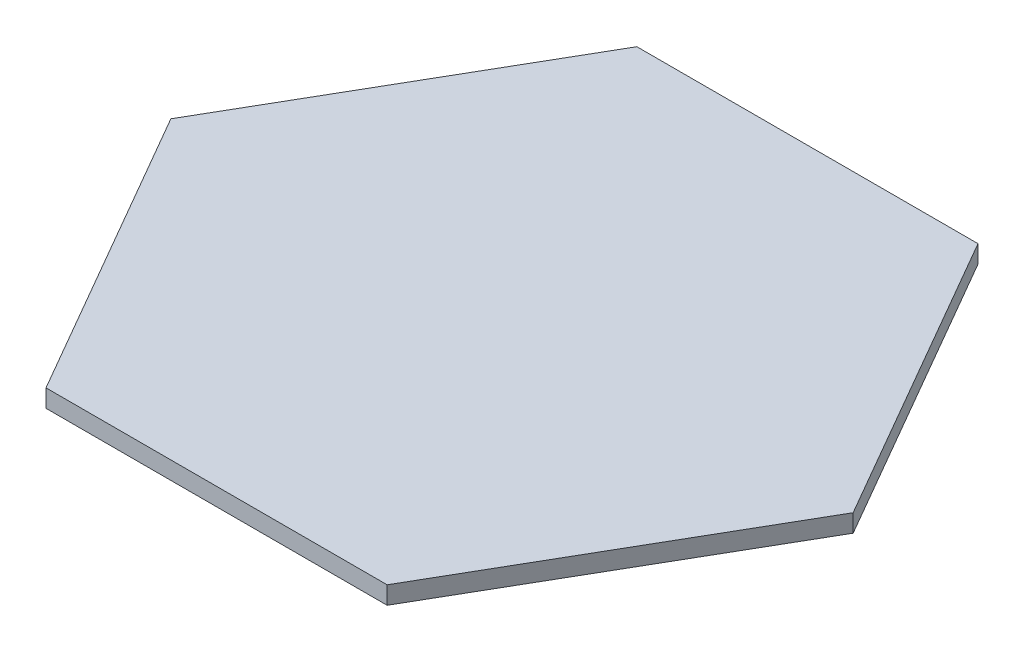
SolidWorks part; units mm, degrees
material "1060 Alloy"
ref_plane "Front Plane" through (0, 0, 0) normal (0, 0, 1) x (1, 0, 0)
ref_plane "Top Plane" through (0, 0, 0) normal (0, 1, 0) x (1, 0, 0)
ref_plane "Right Plane" through (0, 0, 0) normal (1, 0, 0) x (0, 0, -1)
sketch "Sketch1" plane through (0, 0, 0) normal (0, 1, 0) x (1, 0, 0)
  line L0 (61.7779, 1.35) -> (31.2787, 54.1763)
  line L1 (61.7779, 1.35) -> (31.2787, 54.1763) construction
  line L3 (-29.7198, -51.4763) -> (31.2787, -51.4763) construction
  line L4 (-29.7198, 54.1763) -> (-60.2191, 1.35) construction
  line L5 (-60.2191, 1.35) -> (-29.7198, -51.4763) construction
  line L6 (31.2787, 54.1763) -> (-29.7198, 54.1763) construction
  line L7 (31.2787, 54.1763) -> (-29.7198, 54.1763)
  line L8 (-29.7198, 54.1763) -> (-60.2191, 1.35)
  line L9 (-60.2191, 1.35) -> (-29.7198, -51.4763)
  line L10 (-29.7198, -51.4763) -> (31.2787, -51.4763)
  line L11 (31.2787, -51.4763) -> (61.7779, 1.35)
  line L12 (31.2787, -51.4763) -> (61.7779, 1.35) construction
extrude "Boss-Extrude1" add sketch "Sketch1" along normal blind 3.175
